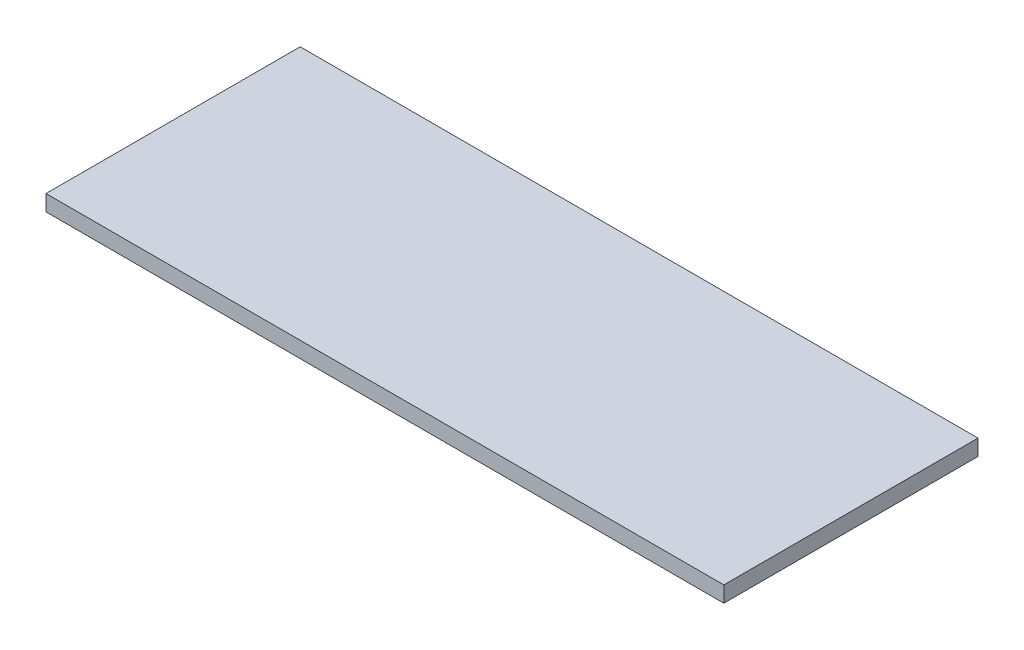
SolidWorks part; units mm, degrees
ref_plane "Front Plane" through (0, 0, 0) normal (0, 0, 1) x (1, 0, 0)
ref_plane "Top Plane" through (0, 0, 0) normal (0, 1, 0) x (1, 0, 0)
ref_plane "Right Plane" through (0, 0, 0) normal (1, 0, 0) x (0, 0, -1)
sketch "Sketch1" plane through (0, 0, 0) normal (0, 1, 0) x (1, 0, 0)
  line L1 (0, 0) -> (203.2, 0)
  line L2 (0, 0) -> (0, -76.2)
  line L3 (0, -76.2) -> (203.2, -76.2)
  line L4 (203.2, 0) -> (203.2, -76.2)
  dimension "D1" = 76.2
  dimension "D2" = 203.2
extrude "Boss-Extrude1" add sketch "Sketch1" along normal blind 4.7625 contours L1 L4 L3 L2
